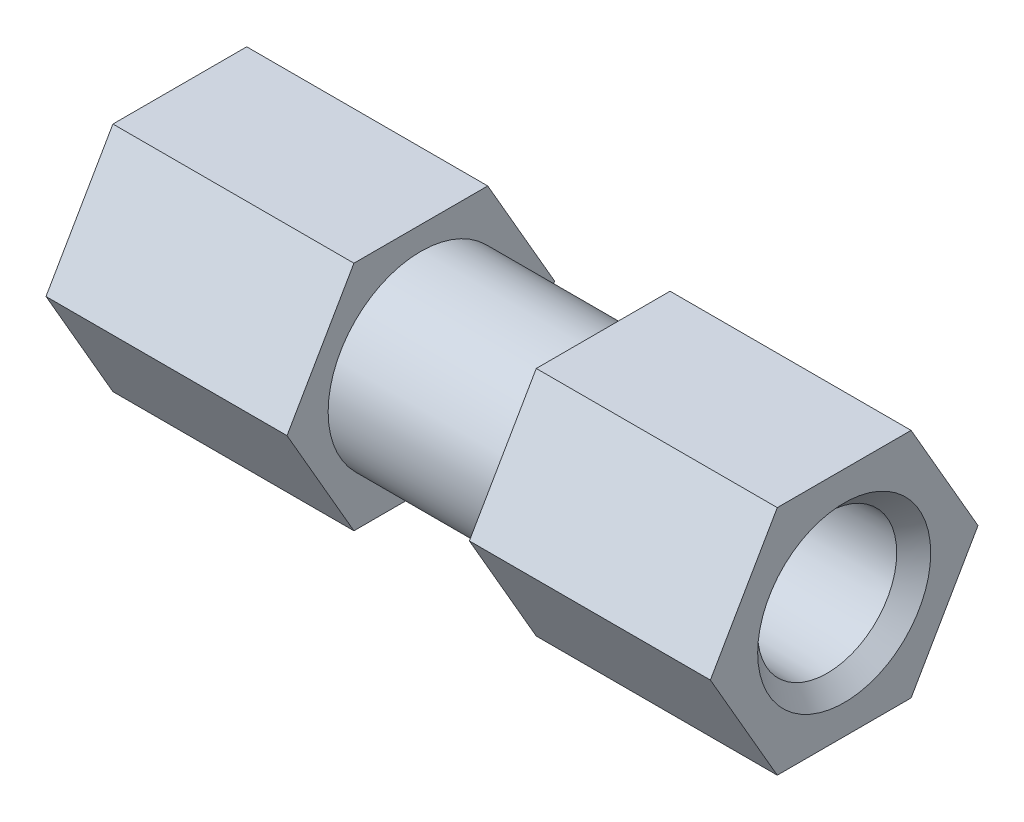
SolidWorks part; units mm, degrees
material "Brass"
ref_plane "Front Plane" through (0, 0, 0) normal (0, 0, 1) x (1, 0, 0)
ref_plane "Top Plane" through (0, 0, 0) normal (0, 1, 0) x (1, 0, 0)
ref_plane "Right Plane" through (0, 0, 0) normal (1, 0, 0) x (0, 0, -1)
ref_plane "Plane1" through (0, 0, 0) normal (-1, 0, 0) x (0, -1, 0)
sketch "Sketch1" plane through (0, 0, 0) normal (-1, 0, 0) x (0, -1, 0)
  line L0 (-9.525, 5.4993) -> (-9.525, -5.4993)
  line L1 (-9.525, -5.4993) -> (0, -10.9985)
  line L2 (0, -10.9985) -> (9.525, -5.4993)
  line L3 (9.525, -5.4993) -> (9.525, 5.4993)
  line L4 (9.525, 5.4993) -> (0, 10.9985)
  line L5 (0, 10.9985) -> (-9.525, 5.4993)
extrude "Boss-Extrude1" add sketch "Sketch1" against normal blind 19.812
sketch "Sketch2" plane through (19.812, 0, 0) normal (1, 0, 0) x (0, 0, -1)
  circle A0 centre (0, 0) radius 7.62
extrude "Boss-Extrude2" add sketch "Sketch2" along normal blind 14.986
ref_plane "Plane2" through (34.798, 0, 0) normal (-1, 0, 0) x (0, -1, 0)
sketch "Sketch3" plane through (34.798, 0, 0) normal (-1, 0, 0) x (0, -1, 0)
  line L0 (9.525, -5.4993) -> (9.525, 5.4993)
  line L1 (9.525, 5.4993) -> (0, 10.9985)
  line L2 (0, 10.9985) -> (-9.525, 5.4993)
  line L3 (-9.525, 5.4993) -> (-9.525, -5.4993)
  line L4 (-9.525, -5.4993) -> (0, -10.9985)
  line L5 (0, -10.9985) -> (9.525, -5.4993)
extrude "Boss-Extrude3" add sketch "Sketch3" against normal blind 19.812
hole_wizard "Hole1" positions "Sketch5" profile "Sketch4" legacy
sketch "Sketch5" plane through (54.61, 0, 0) normal (1, 0, 0) x (0, 0, -1)
  point P0 (0, 0)
sketch "Sketch4" plane through (54.61, 0, 0) normal (0, 1, 0) x (0, 0, -1)
  line L0 (0, 0) -> (0, 9.906)
  line L1 (0, 9.906) -> (5.4966, 9.906)
  line L2 (5.4966, 9.906) -> (5.7508, 0)
  line L3 (5.7508, 0) -> (0, 0)
  line L4 (0, 110) -> (0, -10) construction
  dimension "Minor Diameter" = 10.9933
  dimension "Depth" = 9.906
  dimension "Major Diameter" = 11.5017
hole_wizard "Hole2" positions "Sketch7" profile "Sketch6" legacy
sketch "Sketch7" plane through (0, 0, 0) normal (-1, 0, 0) x (0, 0, 1)
  point P0 (0, 0)
sketch "Sketch6" plane through (0, 0, 0) normal (0, 1, 0) x (0, 0, 1)
  line L0 (0, 0) -> (0, 9.906)
  line L1 (0, 9.906) -> (5.4966, 9.906)
  line L2 (5.4966, 9.906) -> (5.7508, 0)
  line L3 (5.7508, 0) -> (0, 0)
  line L4 (0, 110) -> (0, -10) construction
  dimension "Minor Diameter" = 10.9933
  dimension "Depth" = 9.906
  dimension "Major Diameter" = 11.5017
chamfer "Chamfer1" distance 1.3612 angle 45 2 edges at (54.61, 0, -5.7508) (0, 0, 5.7508)
